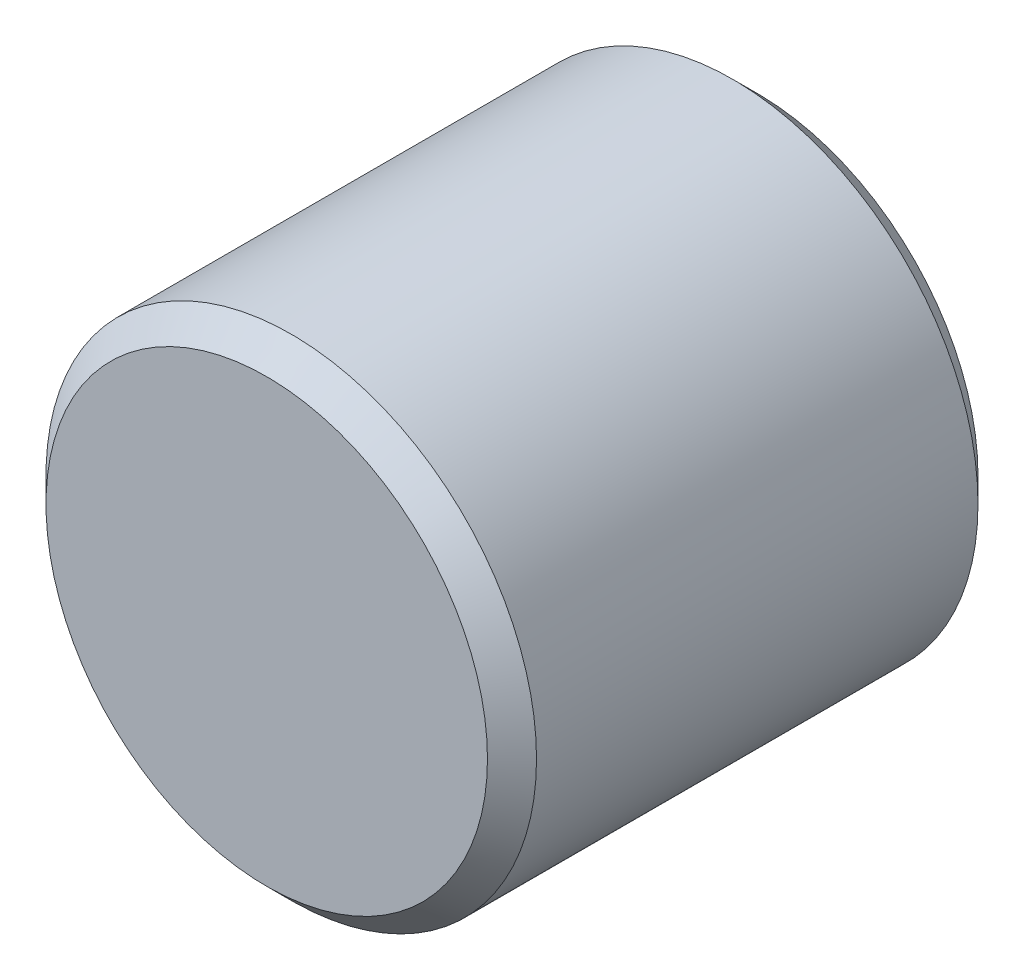
SolidWorks part; units mm, degrees
ref_plane "Front Plane" through (0, 0, 0) normal (0, 0, 1) x (1, 0, 0)
ref_plane "Top Plane" through (0, 0, 0) normal (0, 1, 0) x (1, 0, 0)
ref_plane "Right Plane" through (0, 0, 0) normal (1, 0, 0) x (0, 0, -1)
sketch "Sketch1" plane through (0, 0, 0) normal (0, 0, 1) x (1, 0, 0)
  circle A0 centre (0, 0) radius 1.27
  dimension "D1" = 2.54
extrude "Boss-Extrude1" add sketch "Sketch1" along normal blind 2.54
chamfer "Chamfer1" distance 0.127 angle 45 2 edges at (1.27, 0, 0) (1.27, 0, 2.54)
